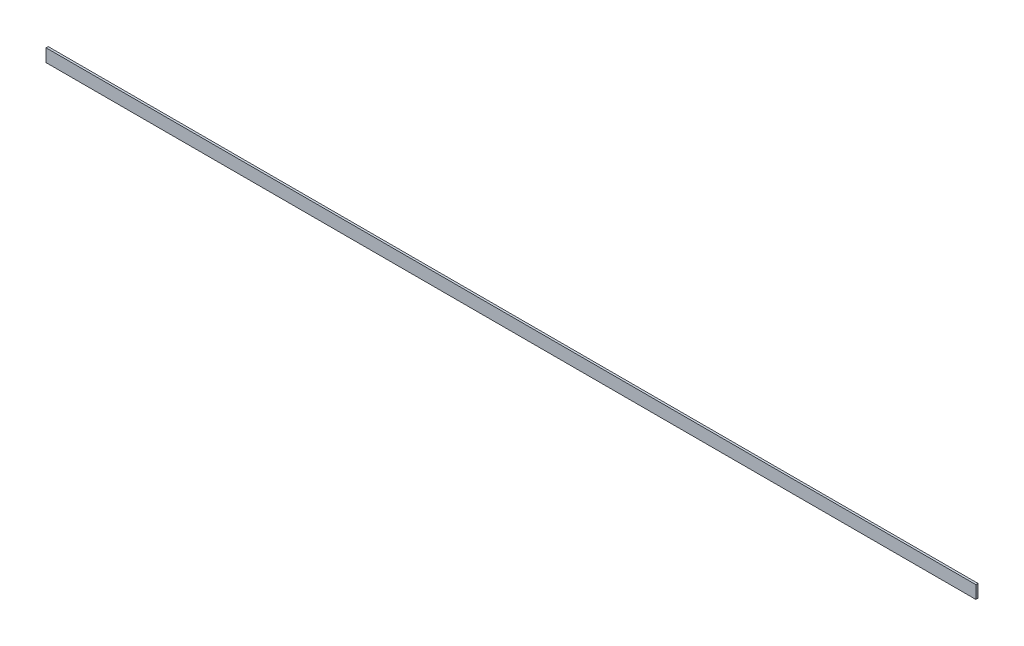
SolidWorks part; units mm, degrees
ref_plane "Спереди" through (0, 0, 0) normal (0, 0, 1) x (1, 0, 0)
ref_plane "Сверху" through (0, 0, 0) normal (0, 1, 0) x (1, 0, 0)
ref_plane "Справа" through (0, 0, 0) normal (1, 0, 0) x (0, 0, -1)
sketch "Эскиз1" plane through (0, 0, 0) normal (1, 0, 0) x (0, 0, -1)
  line L1 (0, 0) -> (5, 0)
  line L2 (0, 0) -> (0, 30)
  line L3 (0, 30) -> (5, 30)
  line L4 (5, 0) -> (5, 30)
extrude "Бобышка-Вытянуть1" add sketch "Эскиз1" along normal blind 2170
